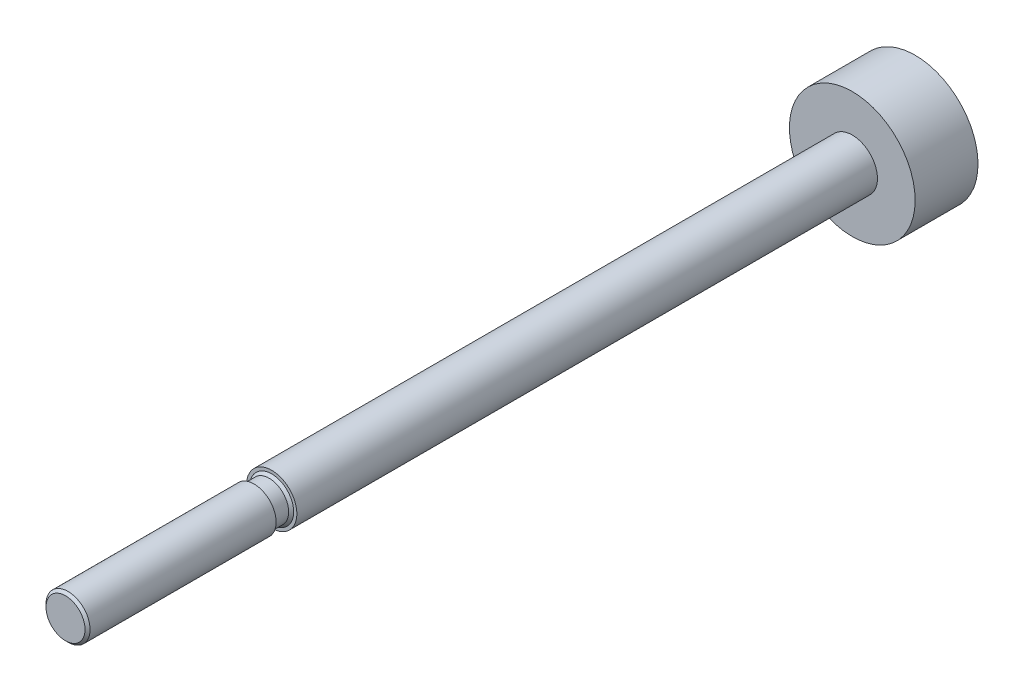
SolidWorks part; units mm, degrees
ref_plane "Front" through (0, 0, 0) normal (0, 0, 1) x (1, 0, 0)
ref_plane "Top" through (0, 0, 0) normal (0, 1, 0) x (1, 0, 0)
ref_plane "Right" through (0, 0, 0) normal (1, 0, 0) x (0, 0, -1)
sketch "Sketch1" plane through (0, 0, 0) normal (0, 0, 1) x (1, 0, 0)
  circle A0 centre (0, 0) radius 2
  dimension "D" = 4
extrude "Base-Extrude" add sketch "Sketch1" along normal up to surface (65.085 mm away)
sketch "Sketch2" plane through (0, 0, 0) normal (0, 0, 1) x (1, 0, 0)
  circle A0 centre (0, 0) radius 5
  dimension "Bore" = 10
extrude "Piston" add sketch "Sketch2" along normal mid plane 5
sketch "Sketch3" plane through (0, 0, 0) normal (1, 0, 0) x (0, 0, -1)
  line L0 (0, 0) -> (-47.8943, 0) construction
  line L1 (-2.5, 0) -> (2.5, 0) construction
  line L2 (-65.085, 1.5525) -> (-64.885, 1.7525)
  line L3 (-65.085, 2) -> (-65.085, -2) construction
  line L4 (-64.885, 1.7525) -> (-50.085, 1.7525)
  line L5 (-50.085, 1.7525) -> (-50.085, 1.55)
  line L6 (-50.085, 1.55) -> (-48.885, 1.55)
  line L8 (-48.885, 1.55) -> (-48.685, 1.75)
  line L10 (-48.685, 1.75) -> (-48.685, 5)
  line L11 (-48.685, 5) -> (-65.085, 5)
  line L12 (-65.085, 5) -> (-65.085, 1.5525)
  line L13 (2.5, 5) -> (-2.5, 5) construction
  dimension "D1" = 0.2
  dimension "D2" = 45
  dimension "D3" = 3.1
  dimension "NN" = 3.505
  dimension "A" = 15
  dimension "D4" = 1.2
revolve "Threads" cut sketch "Sketch3" angle 360 about L0
